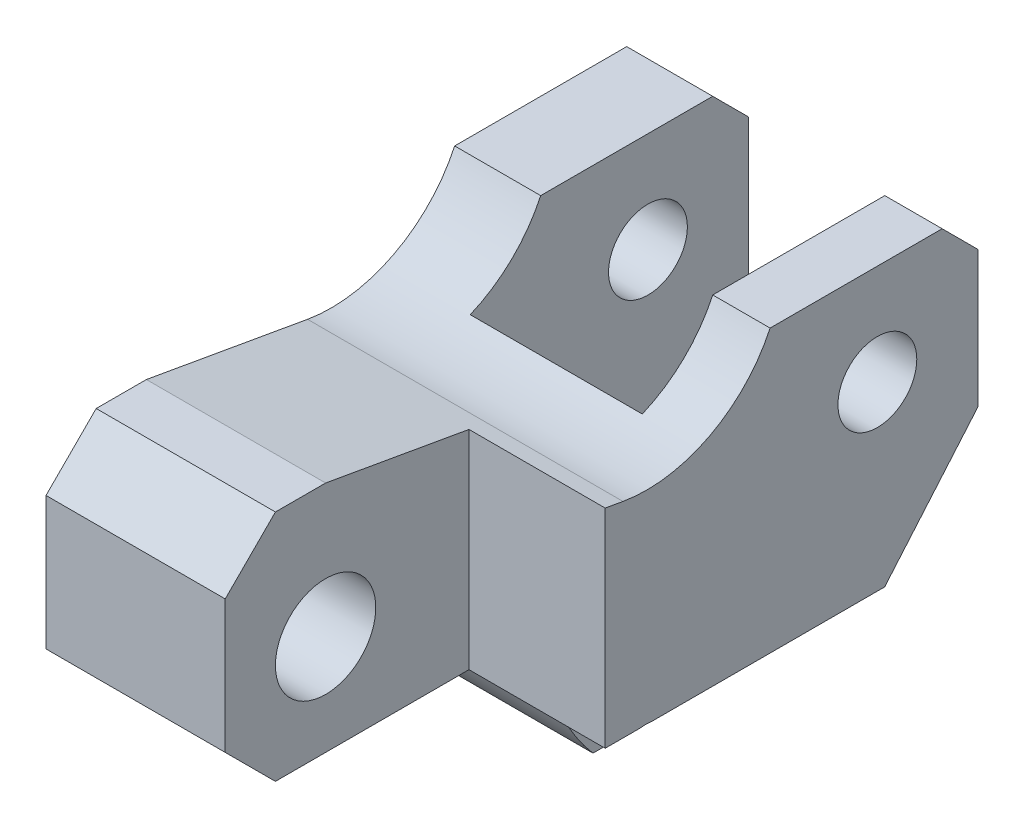
SolidWorks part; units mm, degrees
material "AISI 1020"
ref_plane "Front Plane" through (0, 0, 0) normal (0, 0, 1) x (1, 0, 0)
ref_plane "Top Plane" through (0, 0, 0) normal (0, 1, 0) x (1, 0, 0)
ref_plane "Right Plane" through (0, 0, 0) normal (1, 0, 0) x (0, 0, -1)
sketch "Sketch1" plane through (0, 0, 0) normal (1, 0, 0) x (0, 0, -1)
  line L0 (0, 0) -> (24, 0)
  line L1 (29, -5) -> (29, -24)
  line L2 (24, 0) -> (29, -5)
  line L5 (29, -24) -> (0, -58)
  line L6 (0, -58) -> (-5.703, -58)
  line L7 (-18.1588, -39.2629) -> (-50, -39.2629)
  line L8 (16.2059, -39) -> (16.0887, -38.9154)
  line L9 (16.0887, -38.9154) -> (16.2059, -39)
  line L10 (-57, -32.2629) -> (-57, -13.7176)
  line L13 (-50, -39.2629) -> (-57, -32.2629)
  line L14 (-43, -6.7176) -> (-50, -6.7176)
  line L15 (-57, -13.7176) -> (-50, -6.7176)
  line L16 (-43, -6.7176) -> (-20.5192, -10.6816)
  line L19 (-23, -24) -> (-23, -23.8851)
  line L21 (16.0887, -38.9154) -> (-18.1588, -39.2629)
  arc A0 (-9.519, -52.3876) -> (-5.703, -58) centre (16.2059, -39) ccw
  arc A1 (-9.519, -52.3876) -> (-12.4524, -43.4387) centre (16.2059, -39) cw
  arc A2 (-12.4524, -43.4387) -> (-18.1588, -39.2629) centre (-17.3935, -44.204) ccw
  circle A3 centre (-43, -25.2629) radius 7
  arc A4 (-20.5192, -10.6816) -> (0, 0) centre (-17.2198, 8.0297) ccw
  point P1 (29, 0)
  point P6 (-7.7758, -55.3058)
  point P7 (-57, -39.2629)
  point P19 (-57, -6.7176)
  dimension "D7" = 86
  dimension "D11" = 14
  dimension "D18" = 19
  dimension "D19" = 5
  dimension "D20" = 14
  dimension "D1" = 29
  dimension "D2" = 24
  dimension "D3" = 5
  dimension "D4" = 45
  dimension "D5" = 19
  dimension "D6" = 29
  dimension "D8" = 58
  dimension "D9" = 7
  dimension "D10" = 45
  dimension "D12" = 7
  dimension "D13" = 45
  dimension "D14" = 14
  dimension "D15" = 14
  dimension "D16" = 29
  dimension "D17" = 10
extrude "Boss-Extrude3" add sketch "Sketch1" along normal mid plane 44 contours A3 | A4 L0 L2 L1 L5 L6 A0 A1 A2 L7 L13 L10 L15 L14 L16
sketch "Sketch8" plane through (22, 0, 0) normal (1, 0, 0) x (0, 0, -1)
  circle A0 centre (14.9629, -14) radius 5.5
  dimension "D1" = 11
extrude "Cut-Extrude1" cut sketch "Sketch8" against normal blind 46
sketch "Sketch10" plane through (22, 0, 0) normal (1, 0, 0) x (0, 0, -1)
  line L1 (-18.1588, -39.2629) -> (-50, -39.2629) construction
  line L2 (-57.0591, -6.6658) -> (-23, -6.6658)
  line L3 (-57.0591, -6.6658) -> (-57.0591, -39.2629)
  line L4 (-57.0591, -39.2629) -> (-23, -39.2629)
  line L5 (-23, -6.6658) -> (-23, -39.2629)
  dimension "D1" = 52
extrude "Cut-Extrude2" cut sketch "Sketch10" against normal blind 19 contours L3 L2 L5 L4
sketch "Sketch19" plane through (0, 0, 0) normal (1, 0, 0) x (0, 0, -1)
  line L0 (29, -5) -> (29, 6.7501)
  line L3 (29, -24) -> (0, -58) construction
  arc A1 (18.7647, -36) -> (-9.8257, -9.4725) centre (29, 3.7019) cw
  arc A2 (-20.5192, -10.6816) -> (0, 0) centre (-17.2198, 8.0297) ccw construction
  circle A3 centre (29, 3.7019) radius 41
  dimension "D1" = 41
extrude "Cut-Extrude5" cut sketch "Sketch19" against normal blind 10 and the other way blind 14 contours A3
sketch "Sketch21" plane through (22, 0, 0) normal (1, 0, 0) x (0, 0, -1)
  line L1 (-23, -39.2629) -> (16.0401, -39.2629)
  line L2 (-23, -39.2629) -> (-23, -58.2629)
  line L3 (-23, -58.2629) -> (16.0401, -58.2629)
  line L4 (16.0401, -39.2629) -> (16.0401, -58.2629)
extrude "Cut-Extrude7" cut sketch "Sketch21" against normal blind 19
